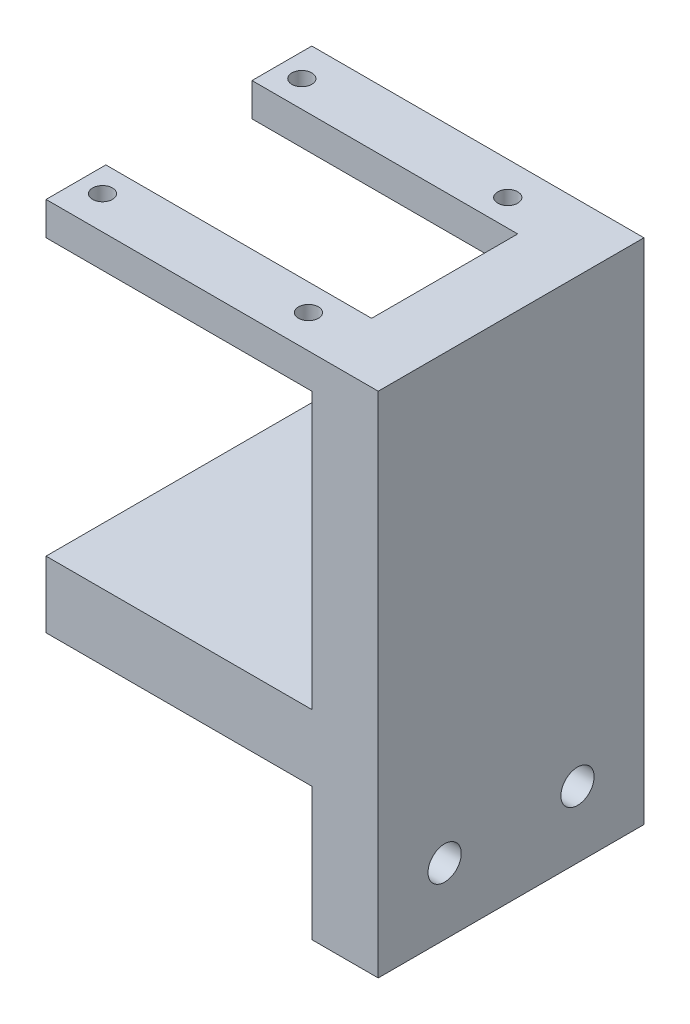
SolidWorks part; units mm, degrees
ref_plane "Front Plane" through (0, 0, 0) normal (0, 0, 1) x (1, 0, 0)
ref_plane "Top Plane" through (0, 0, 0) normal (0, 1, 0) x (1, 0, 0)
ref_plane "Right Plane" through (0, 0, 0) normal (1, 0, 0) x (0, 0, -1)
sketch "Sketch1" plane through (0, 0, 0) normal (1, 0, 0) x (0, 0, -1)
  line L0 (0, 55) -> (0, -55) construction
  line L5 (-20, 56.5) -> (20, 56.5)
  line L6 (-20, 56.5) -> (-20, 0)
  line L7 (-20, 0) -> (20, 0)
  line L8 (20, 56.5) -> (20, 0)
  line L9 (-20, 56.5) -> (20, 0) construction
  line L10 (-20, 0) -> (20, 56.5) construction
  line L11 (55, 0) -> (-55, 0) construction
  line L13 (-20, -20) -> (20, -20)
  line L14 (-20, -20) -> (-20, 0)
  line L15 (-20, 0) -> (20, 0)
  line L16 (20, -20) -> (20, 0)
  line L17 (-20, -20) -> (20, 0) construction
  line L18 (-20, 0) -> (20, -20) construction
  line L19 (10, -15) -> (-10, -15) construction
  line L20 (10, -15) -> (10, -5) construction
  line L21 (10, -5) -> (-10, -5) construction
  line L22 (-10, -15) -> (-10, -5) construction
  line L23 (10, -15) -> (-10, -5) construction
  line L24 (10, -5) -> (-10, -15) construction
  circle A0 centre (-10, -10) radius 2.5
  circle A1 centre (10, -10) radius 2.5
  point P1 (0, 28.25)
  point P10 (0, -10)
  point P11 (0, -10)
  dimension "D5" = 5
  dimension "D1" = 56.5
  dimension "D2" = 40
  dimension "D3" = 20
  dimension "D4" = 20
extrude "Boss-Extrude1" add sketch "Sketch1" along normal blind 10 contours L8 L5 L6 L7 | L13 L16 L7 L14 A1 A0
sketch "Sketch3" plane through (0, 0, 0) normal (-1, 0, 0) x (0, 0, 1)
  line L0 (20, 56.5) -> (20, -20) construction
  line L1 (-20, 10) -> (20, 10)
  line L2 (-20, 10) -> (-20, 0)
  line L3 (-20, 0) -> (20, 0)
  line L4 (20, 10) -> (20, 0)
  line L5 (-20, 10) -> (20, 0) construction
  line L6 (-20, 0) -> (20, 10) construction
  dimension "D1" = 10
extrude "Boss-Extrude2" add sketch "Sketch3" along normal blind 40
sketch "Sketch4" plane through (0, 0, 0) normal (-1, 0, 0) x (0, 0, 1)
  line L13 (-20, 56.5) -> (-11, 56.5)
  line L14 (-20, 56.5) -> (-20, 51.5)
  line L15 (-20, 51.5) -> (-11, 51.5)
  line L16 (-11, 56.5) -> (-11, 51.5)
  dimension "D1" = 9
  dimension "D2" = 5
extrude "Boss-Extrude3" add sketch "Sketch4" along normal blind 40
sketch "Sketch5" plane through (0, 56.5, 0) normal (0, 1, 0) x (1, 0, 0)
  line L1 (-40, 20) -> (-36.5, 20) construction
  line L2 (-40, 20) -> (-40, 15) construction
  line L3 (-40, 15) -> (-36.5, 15) construction
  line L4 (-36.5, 20) -> (-36.5, 15) construction
  line L5 (10, 20) -> (-40, 20) construction
  line L7 (-0.5, 20) -> (-5.5, 20) construction
  line L8 (-0.5, 20) -> (-0.5, 15) construction
  line L9 (-0.5, 15) -> (-5.5, 15) construction
  line L10 (-5.5, 20) -> (-5.5, 15) construction
  circle A0 centre (-36.5, 15) radius 1.5
  circle A1 centre (-5.5, 15) radius 1.5
  dimension "D3" = 3
  dimension "D7" = 3
  dimension "D1" = 3.5
  dimension "D2" = 5
  dimension "D4" = 5
  dimension "D5" = 5
  dimension "D6" = 31
extrude "Cut-Extrude1" cut sketch "Sketch5" against normal up to next (5 mm away)
mirror "Mirror2" about plane through (0, 0, 0) normal (0, 0, 1) of "Cut-Extrude1", "Boss-Extrude3"
